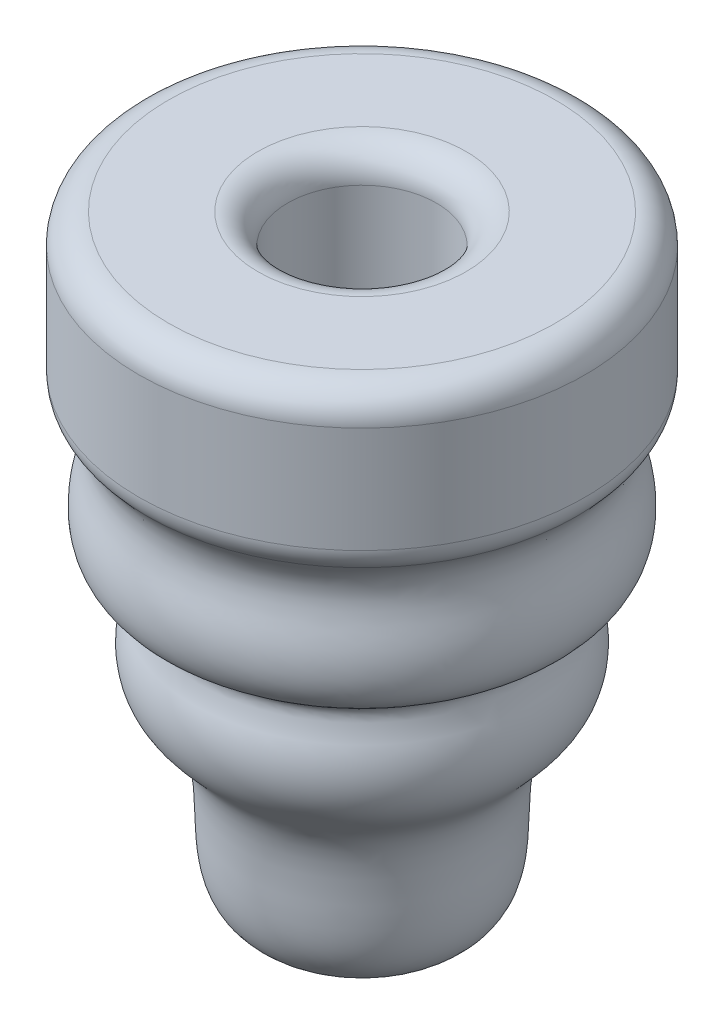
SolidWorks part; units mm, degrees
ref_plane "Front Plane" through (0, 0, 0) normal (0, 0, 1) x (1, 0, 0)
ref_plane "Top Plane" through (0, 0, 0) normal (0, 1, 0) x (1, 0, 0)
ref_plane "Right Plane" through (0, 0, 0) normal (1, 0, 0) x (0, 0, -1)
sketch "Sketch1" plane through (0, 0, 0) normal (0, 0, 1) x (1, 0, 0)
  line L0 (0, 80.0042) -> (0, -42.6607) construction
sketch "Sketch2" plane through (0, 0, 0) normal (1, 0, 0) x (0, 0, -1)
  line L0 (0, 0) -> (0, 18.6718)
  line L1 (0, 200080.0042) -> (0, -200042.6607) construction
  line L2 (0, 18.6718) -> (6.35, 18.6718)
  line L3 (6.35, 18.6718) -> (6.35, 28.8318)
  line L4 (8.89, 31.3718) -> (16.51, 31.3718)
  line L5 (19.05, 28.8318) -> (19.05, 19.7836)
  line L8 (0, -21.0748) -> (0, 0)
  arc A0 (19.05, 28.8318) -> (16.51, 31.3718) centre (16.51, 28.8318) ccw
  arc A1 (8.89, 31.3718) -> (6.35, 28.8318) centre (8.89, 28.8318) ccw
  arc A2 (18.3245, 18.0061) -> (19.05, 19.7836) centre (16.51, 19.7836) ccw
  spline S0 degree 3 poles (18.3245, 18.0061) (16.5543, 16.1992) (16.8487, 13.9639) (17.9431, 10.1641) (17.7068, 6.2097) (13.1158, 4.7851) (15.2558, 0.708) (14.7192, -3.7155) (6.5817, -9.8871) (14.3244, -22.1215) (0, -21.0748) knots 0.013384 0.013384 0.013384 0.013384 0.124755 0.165583 0.268611 0.337747 0.396161 0.508807 0.60397 1 1 1 1
  point P13 (19.05, 31.3718)
  point P16 (6.35, 31.3718)
  dimension "D7" = 2.54
  dimension "D1" = 2.54
  dimension "D2" = 6.35
  dimension "D3" = 12.7
  dimension "D5" = 12.7
revolve "Revolve1" add sketch "Sketch2" angle 360 about L0
